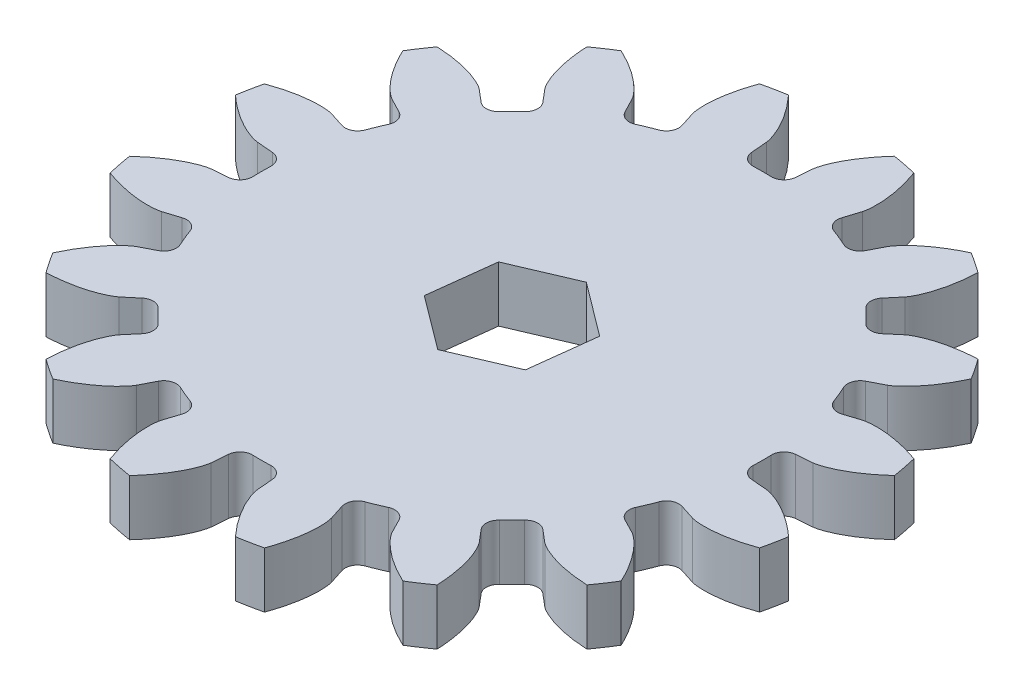
SolidWorks part; units mm, degrees
ref_plane "Front Plane" through (0, 0, 0) normal (0, 0, 1) x (1, 0, 0)
ref_plane "Top Plane" through (0, 0, 0) normal (0, 1, 0) x (1, 0, 0)
ref_plane "Right Plane" through (0, 0, 0) normal (1, 0, 0) x (0, 0, -1)
sketch "Sketch1" plane through (0, 0, 0) normal (0, 1, 0) x (1, 0, 0)
  circle A0 centre (0, 0) radius 38.1
  dimension "D1" = 76.2
extrude "Boss-Extrude1" add sketch "Sketch1" along normal blind 6.35
sketch "Sketch2" plane through (0, 6.35, 0) normal (0, 1, 0) x (1, 0, 0)
  line L0 (31.714, 2.647) -> (28.476, 2.3767)
  line L1 (31.714, -2.647) -> (28.476, -2.3767)
  line L2 (0, 0) -> (31.714, 2.647) construction
  line L3 (0, 0) -> (31.714, -2.647) construction
  arc A0 (37.6172, -6.0462) -> (37.6172, 6.0462) centre (0, 0) ccw
  circle A1 centre (0, 0) radius 33.8667 construction
  circle A2 centre (0, 0) radius 31.8243 construction
  circle A3 centre (0, 0) radius 28.575 construction
  arc A4 (28.476, -2.3767) -> (28.476, 2.3767) centre (0, 0) ccw
  spline S0 degree 4 poles (31.714, 2.647) (31.7241, 2.6479) (31.7526, 2.6512) (31.8061, 2.659) (31.8932, 2.6741) (32.0036, 2.6971) (32.1457, 2.7308) (32.3122, 2.7758) (32.4941, 2.8308) (32.6908, 2.8965) (32.8859, 2.9673) (33.0793, 3.0428) (33.2709, 3.1223) (33.5017, 3.2237) (33.7764, 3.3523) (34.0945, 3.513) (34.4516, 3.7072) (34.8112, 3.918) (35.1615, 4.1357) (35.5111, 4.3677) (35.8461, 4.6005) (36.1893, 4.8543) (36.5037, 5.0947) (36.8504, 5.3771) (37.1285, 5.6089) (37.4891, 5.9284) (37.7002, 6.1212) (37.945, 6.3515) (38.0525, 6.4563) (38.1188, 6.5207) knots 0 0 0 0 0 0.005377 0.015084 0.028532 0.04661 0.064855 0.092111 0.119476 0.146842 0.174209 0.201575 0.228941 0.256307 0.307035 0.361767 0.4165 0.471232 0.525964 0.580697 0.635429 0.690161 0.744894 0.799626 0.854358 0.909091 0.954545 1 1 1 1 1 construction
  spline S1 degree 4 poles (31.714, 2.647) (31.7241, 2.6479) (31.7526, 2.6512) (31.8061, 2.659) (31.8932, 2.6741) (32.0036, 2.6971) (32.1457, 2.7308) (32.3122, 2.7758) (32.4941, 2.8308) (32.6908, 2.8965) (32.8859, 2.9673) (33.0793, 3.0428) (33.2709, 3.1223) (33.5017, 3.2237) (33.7764, 3.3523) (34.0945, 3.513) (34.4516, 3.7072) (34.8112, 3.918) (35.1615, 4.1357) (35.5111, 4.3677) (35.8461, 4.6005) (36.1893, 4.8543) (36.5037, 5.0947) (36.8504, 5.3771) (37.1285, 5.6089) (37.4109, 5.8591) (37.5476, 5.9825) (37.6172, 6.0462) knots 0 0 0 0 0 0.005377 0.015084 0.028532 0.04661 0.064855 0.092111 0.119476 0.146842 0.174209 0.201575 0.228941 0.256307 0.307035 0.361767 0.4165 0.471232 0.525964 0.580697 0.635429 0.690161 0.744894 0.799626 0.854358 0.909091 0.909091 0.909091 0.909091 0.909091
  spline S2 degree 4 poles (31.714, -2.647) (31.7241, -2.6479) (31.7526, -2.6512) (31.8061, -2.659) (31.8932, -2.6741) (32.0036, -2.6971) (32.1457, -2.7308) (32.3122, -2.7758) (32.4941, -2.8308) (32.6908, -2.8965) (32.8859, -2.9673) (33.0793, -3.0428) (33.2709, -3.1223) (33.5017, -3.2237) (33.7764, -3.3523) (34.0945, -3.513) (34.4516, -3.7072) (34.8112, -3.918) (35.1615, -4.1357) (35.5111, -4.3677) (35.8461, -4.6005) (36.1893, -4.8543) (36.5037, -5.0947) (36.8504, -5.3771) (37.1285, -5.6089) (37.4891, -5.9284) (37.7002, -6.1212) (37.945, -6.3515) (38.0525, -6.4563) (38.1188, -6.5207) knots 0 0 0 0 0 0.005377 0.015084 0.028532 0.04661 0.064855 0.092111 0.119476 0.146842 0.174209 0.201575 0.228941 0.256307 0.307035 0.361767 0.4165 0.471232 0.525964 0.580697 0.635429 0.690161 0.744894 0.799626 0.854358 0.909091 0.954545 1 1 1 1 1 construction
  spline S3 degree 4 poles (31.714, -2.647) (31.7241, -2.6479) (31.7526, -2.6512) (31.8061, -2.659) (31.8932, -2.6741) (32.0036, -2.6971) (32.1457, -2.7308) (32.3122, -2.7758) (32.4941, -2.8308) (32.6908, -2.8965) (32.8859, -2.9673) (33.0793, -3.0428) (33.2709, -3.1223) (33.5017, -3.2237) (33.7764, -3.3523) (34.0945, -3.513) (34.4516, -3.7072) (34.8112, -3.918) (35.1615, -4.1357) (35.5111, -4.3677) (35.8461, -4.6005) (36.1893, -4.8543) (36.5037, -5.0947) (36.8504, -5.3771) (37.1285, -5.6089) (37.4109, -5.8591) (37.5476, -5.9825) (37.6172, -6.0462) knots 0 0 0 0 0 0.005377 0.015084 0.028532 0.04661 0.064855 0.092111 0.119476 0.146842 0.174209 0.201575 0.228941 0.256307 0.307035 0.361767 0.4165 0.471232 0.525964 0.580697 0.635429 0.690161 0.744894 0.799626 0.854358 0.909091 0.909091 0.909091 0.909091 0.909091
  dimension "D2" = 67.7333
  dimension "D3" = 63.6485
  dimension "D4" = 57.15
extrude "Cut-Extrude1" cut sketch "Sketch2" against normal up to next (6.35 mm away)
fillet "Fillet1" radius 1.4203 2 edges at (28.476, 3.175, 2.3767) (28.476, 3.175, -2.3767)
ref_axis "Axis1" through (0, 6.35, 0) along (0, -1, 0)
pattern_circular "CirPattern2" count 16 over 360 about axis through (0, 6.35, 0) along (0, -1, 0) of "Cut-Extrude1", "Fillet1"
sketch "Sketch3" plane through (0, 6.35, 0) normal (0, 1, 0) x (1, 0, 0)
  line L1 (-0.9082, -7.5714) -> (6.1029, -4.5722)
  line L2 (6.1029, -4.5722) -> (7.0111, 2.9992)
  line L3 (7.0111, 2.9992) -> (0.9082, 7.5714)
  line L4 (0.9082, 7.5714) -> (-6.1029, 4.5722)
  line L5 (-6.1029, 4.5722) -> (-7.0111, -2.9992)
  line L6 (-7.0111, -2.9992) -> (-0.9082, -7.5714)
  circle A0 centre (0, 0) radius 6.604 construction
extrude "Cut-Extrude2" cut sketch "Sketch3" against normal up to next
equation "\"DiametralPitch\" = 6"
equation "\"NumTeeth\" = 16"
equation "\"PressureAngle\"= 20"
equation "\"Addendum\"= 1 / \"DiametralPitch\""
equation "\"Dedendum\"= 1.25 / \"DiametralPitch\""
equation "\"WorkingDepth\"= 2 / \"DiametralPitch\""
equation "\"WholeDepth\"= 2.25 / \"DiametralPitch\""
equation "\"Clearance\"= 0.25 / \"DiametralPitch\""
equation "\"ToothThickness\"= 1.5708 / \"DiametralPitch\""
equation "\"CircularPitch\"= pi / \"DiametralPitch\""
equation "\"PitchCircle\"= \"NumTeeth\" / \"DiametralPitch\""
equation "\"OutsideDiameter\"= ( \"NumTeeth\" + 2 ) / \"DiametralPitch\""
equation "\"Fillet\"= \"Clearance\" * cos ( \"PressureAngle\" ) * tan ( ( 90 + \"PressureAngle\" ) / 2 )"
equation "\"AddendumCircle\"= \"PitchCircle\" + ( 2 * \"Addendum\" )"
equation "\"DedendumCircle\" = \"PitchCircle\" - ( 2 * \"Dedendum\" )"
equation "\"BaseCircle\"= \"PitchCircle\" * cos ( \"PressureAngle\" )"
equation "\"PitchAngle\"= 360deg / \"NumTeeth\""
equation "\"Alpha\"= sqr ( \"PitchCircle\" ^ 2 - \"BaseCircle\" ^ 2 ) / \"BaseCircle\" * 180 / PI - \"PressureAngle\""
equation "\"Beta\"= ( \"PitchAngle\" / 4 - \"Alpha\" )"
equation "\"Phi\"= sqr ( ( \"AddendumCircle\" / 2 ) ^ 2 - ( \"BaseCircle\" / 2 ) ^ 2 ) / ( \"BaseCircle\" / 2 )"
equation "\"D1@Sketch1\"=\"OutsideDiameter\""
equation "\"D2@Sketch2\"=\"PitchCircle\""
equation "\"D3@Sketch2\"=\"BaseCircle\""
equation "\"D4@Sketch2\"=\"DedendumCircle\""
equation "\"D1@Fillet1\"=\"Fillet\""
equation "\"D1@CirPattern2\"=\"NumTeeth\""
